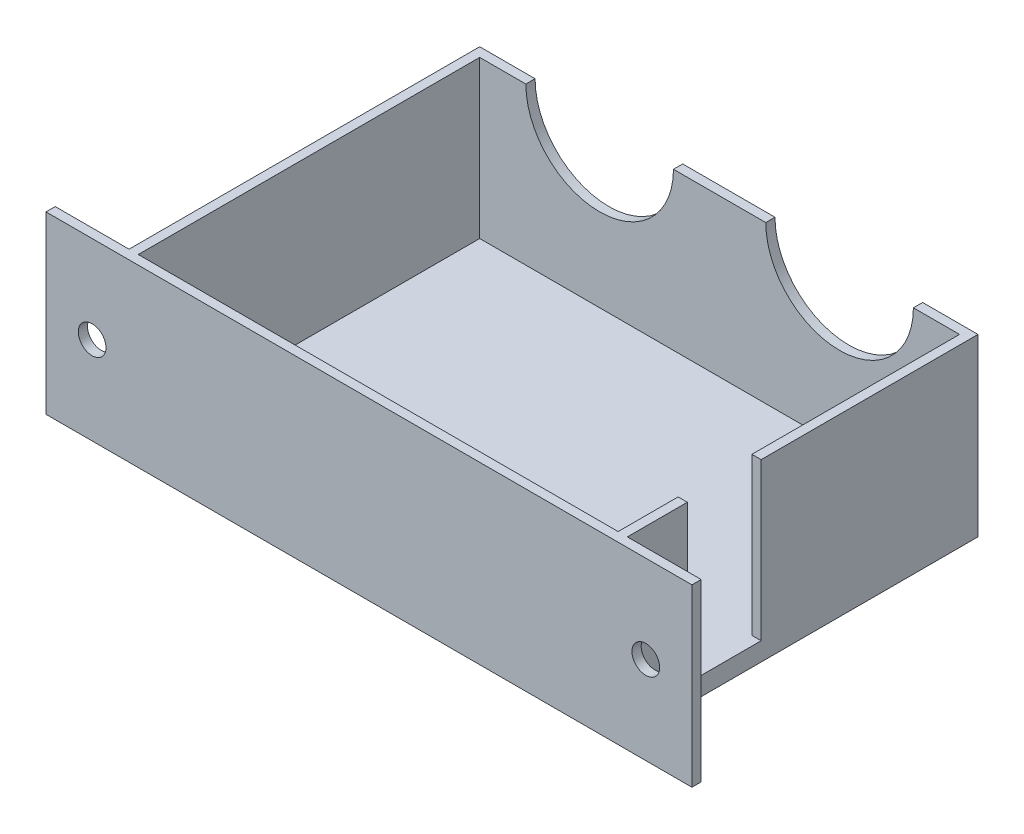
SolidWorks part; units mm, degrees
ref_plane "Front Plane" through (0, 0, 0) normal (0, 0, 1) x (1, 0, 0)
ref_plane "Top Plane" through (0, 0, 0) normal (0, 1, 0) x (1, 0, 0)
ref_plane "Right Plane" through (0, 0, 0) normal (1, 0, 0) x (0, 0, -1)
sketch "Sketch1" plane through (0, 0, 0) normal (0, 1, 0) x (1, 0, 0)
  line L0 (54, 0) -> (62, 0)
  line L1 (0, 0) -> (54, 0)
  line L2 (0, 1) -> (0, 39)
  line L3 (0, 39) -> (54, 39)
  line L4 (54, 1) -> (54, 39)
  line L5 (1, 1) -> (53, 1)
  line L6 (1, 1) -> (1, 38)
  line L7 (1, 38) -> (53, 38)
  line L8 (53, 1) -> (53, 38)
  line L9 (62, 0) -> (62, 1)
  line L10 (62, 1) -> (54, 1)
  line L11 (0, 0) -> (-8, 0)
  line L12 (-8, 0) -> (-8, 1)
  line L13 (-8, 1) -> (0, 1)
  point P11 (27, 1)
  point P12 (27, 0)
  dimension "D1" = 39
  dimension "D2" = 54
  dimension "D3" = 52
  dimension "D4" = 37
  dimension "D5" = 70
extrude "Boss-Extrude1" add sketch "Sketch1" along normal blind 19
ref_plane "Plane1" through (0, 0, 0) normal (0, 0, 1) x (1, 0, 0)
sketch "Sketch2" plane through (0, 0, 0) normal (0, 0, 1) x (1, 0, 0)
  line L0 (-3, 9.5) -> (57, 9.5) construction
  line L1 (-8, 19) -> (62, 19) construction
  line L2 (-8, 19) -> (-8, 0) construction
  circle A0 centre (-3, 9.5) radius 1.5
  circle A1 centre (57, 9.5) radius 1.5
  point P6 (27, 19)
  point P7 (27, 9.5)
  point P10 (-8, 9.5)
  dimension "D1" = 60
  dimension "D2" = 3
extrude "Cut-Extrude1" cut sketch "Sketch2" against normal up to next
sketch "Sketch3" plane through (0, 0, 0) normal (0, 1, 0) x (1, 0, 0)
  line L0 (53, 1) -> (53, 38) construction
  line L5 (1, 38) -> (53, 38)
  line L6 (1, 38) -> (1, 1)
  line L7 (1, 1) -> (53, 1)
  line L8 (53, 38) -> (53, 1)
  line L9 (1, 1) -> (53, 1) construction
  dimension "D1" = 0
extrude "Boss-Extrude2" add sketch "Sketch3" along normal blind 2
ref_plane "Plane2" through (0, 0, -39) normal (0, 0, -1) x (-1, 0, 0)
sketch "Sketch4" plane through (0, 0, -39) normal (0, 0, -1) x (-1, 0, 0)
  line L0 (-54, 19) -> (0, 19) construction
  line L1 (-14, 19) -> (-40, 19) construction
  circle A0 centre (-14, 19) radius 8
  circle A1 centre (-40, 19) radius 8
  point P6 (-27, 19)
  point P7 (-27, 19)
  dimension "D1" = 16
  dimension "D2" = 26
extrude "Cut-Extrude2" cut sketch "Sketch4" against normal up to next
ref_plane "Plane3" through (54, 0, 0) normal (1, 0, 0) x (0, 0, -1)
sketch "Sketch5" plane through (54, 0, 0) normal (1, 0, 0) x (0, 0, -1)
  line L0 (1, 19) -> (39, 19) construction
  line L1 (7.5, 19) -> (15.5, 19)
  line L2 (7.5, 19) -> (7.5, 2)
  line L3 (7.5, 2) -> (15.5, 2)
  line L4 (15.5, 19) -> (15.5, 2)
  line L5 (0, 10.45) -> (0, -10.45) construction
  dimension "D1" = 7.5
  dimension "D2" = 8
  dimension "D3" = 17
extrude "Cut-Extrude3" cut sketch "Sketch5" against normal blind 1
